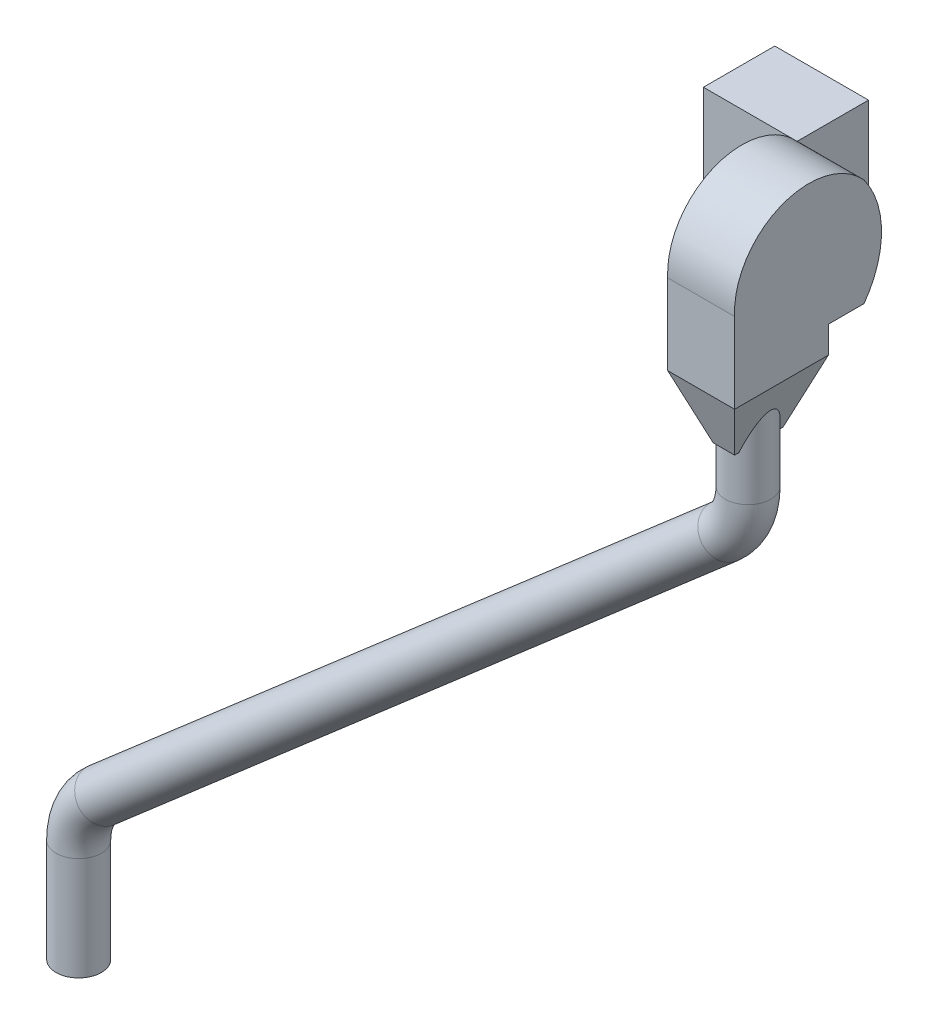
SolidWorks part; units mm, degrees
ref_plane "Alzado" through (0, 0, 0) normal (0, 0, 1) x (1, 0, 0)
ref_plane "Planta" through (0, 0, 0) normal (0, 1, 0) x (1, 0, 0)
ref_plane "Vista lateral" through (0, 0, 0) normal (1, 0, 0) x (0, 0, -1)
sketch "Croquis1" plane through (0, 0, 0) normal (0, 0, 1) x (1, 0, 0)
  line L1 (-105, -120) -> (105, -120)
  line L2 (-105, -120) -> (-105, 120)
  line L3 (-105, 120) -> (105, 120)
  line L4 (105, -120) -> (105, 120)
  line L5 (-105, -120) -> (105, 120) construction
  line L6 (-105, 120) -> (105, -120) construction
  point P0 (0, 0)
  dimension "D1" = 210
  dimension "D2" = 240
extrude "Saliente-Extruir1" add sketch "Croquis1" along normal blind 160
sketch "Croquis2" plane through (105, 0, 0) normal (1, 0, 0) x (0, 0, -1)
  line L0 (-160, -120) -> (-450, -120)
  line L1 (-450, -120) -> (-450, 0)
  arc A0 (-450, 0) -> (-160, 120) centre (-283.7057, 8.5387) cw
  arc A1 (-160, -120) -> (-160, 120) centre (-324.1232, 0) ccw
  dimension "D1" = 450
extrude "Saliente-Extruir2" add sketch "Croquis2" along normal blind 150 separate body
sketch "Croquis3" plane through (0, -120, 0) normal (0, -1, 0) x (1, 0, 0)
  line L0 (105, 450) -> (255, 450)
  line L1 (255, 450) -> (255, 239.8579)
  line L2 (255, 450) -> (255, 160) construction
  line L3 (255, 239.8579) -> (105, 239.8579)
  line L4 (105, 450) -> (105, 160) construction
  line L5 (105, 239.8579) -> (105, 450)
extrude "Saliente-Extruir3" add sketch "Croquis3" along normal blind 60
sketch "Croquis4" plane through (0, -180, 0) normal (0, -1, 0) x (1, 0, 0)
  circle A0 centre (180, 344.9289) radius 50.8
  dimension "D1" = 101.6
extrude "Saliente-Extruir4" add sketch "Croquis4" along normal blind 170
sketch "Croquis5" plane through (0, -180, 0) normal (0, -1, 0) x (1, 0, 0)
  line L0 (105, 450) -> (255, 450)
  line L1 (255, 450) -> (255, 239.8579)
  line L2 (255, 239.8579) -> (105, 239.8579)
  line L3 (105, 239.8579) -> (105, 450)
extrude "Saliente-Extruir5" add sketch "Croquis5" along normal blind 140 draft 20
sketch3d "Croquis3D1"
  line L0 (180, -350, 344.9289) -> (180, -419.3736, 344.9289)
  line L2 (180, -350, 344.9289) -> (180, -320, 344.9289) construction
  line L4 (-1320, -1987.868, 344.9289) -> (-1320, -1856.3623, 344.9289)
  line L5 (-1268.2396, -1743.0089, 344.9289) -> (128.2396, -532.727, 344.9289)
  arc A0 (-1320, -1856.3623, 344.9289) -> (-1268.2396, -1743.0089, 344.9289) centre (-1170, -1856.3623, 344.9289) ccw
  arc A1 (180, -419.3736, 344.9289) -> (128.2396, -532.727, 344.9289) centre (30, -419.3736, 344.9289) ccw
  point P6 (-1320, -1787.868, 344.9289)
  point P7 (-1170, -1856.3623, 194.9289)
  point P8 (-1320, -2050, 344.9289)
  point P12 (180, -550, 344.9289)
  point P13 (180, -487.868, 344.9289)
  point P16 (30, -419.3736, 194.9289)
  dimension "D1" = 200
  dimension "D2" = 150
  dimension "D3" = 150
  dimension "D4" = 200
  dimension "D5" = 2121.3203
sketch "Croquis6" plane through (0, -350, 0) normal (0, -1, 0) x (1, 0, 0)
  circle A0 centre (180, 344.9289) radius 50.8
sweep "Barrer1" add profiles "Croquis6" path "Croquis3D1"
sketch "Croquis7" plane through (0, -1987.868, 0) normal (0, -1, 0) x (1, 0, 0)
  circle A0 centre (-1320, 344.9289) radius 50.8
extrude "Saliente-Extruir6" add sketch "Croquis7" along normal blind 100
